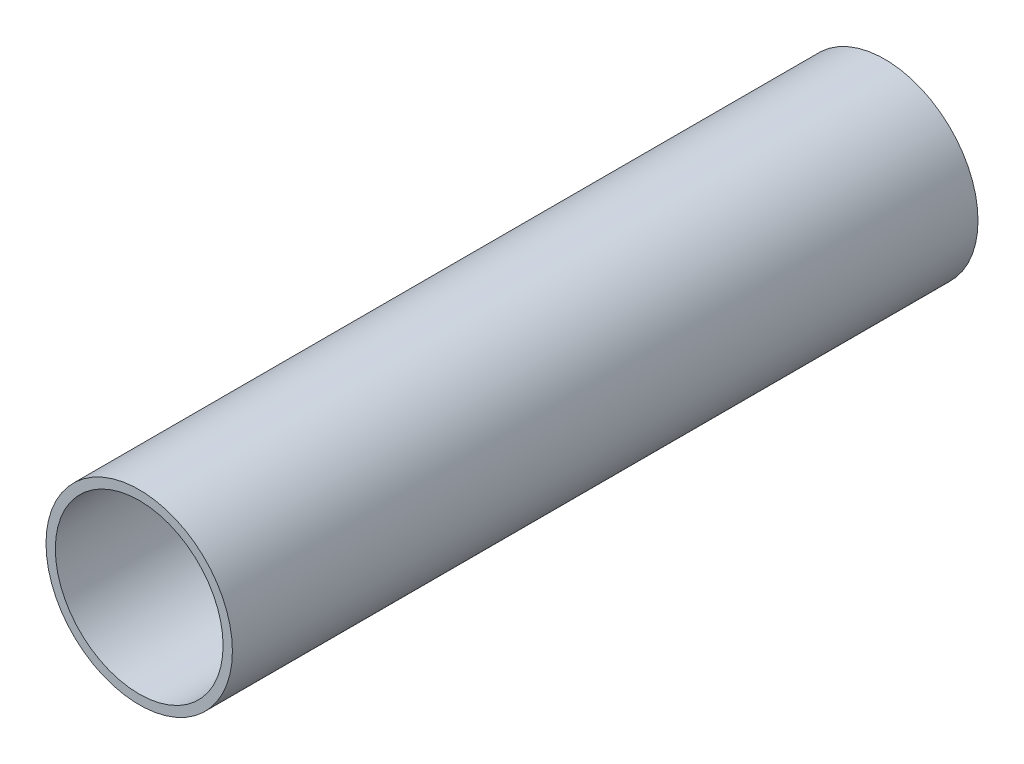
SolidWorks part; units mm, degrees
ref_plane "Front Plane" through (0, 0, 0) normal (0, 0, 1) x (1, 0, 0)
ref_plane "Top Plane" through (0, 0, 0) normal (0, 1, 0) x (1, 0, 0)
ref_plane "Right Plane" through (0, 0, 0) normal (1, 0, 0) x (0, 0, -1)
sketch "Sketch1" plane through (0, 0, 0) normal (0, 0, 1) x (1, 0, 0)
  circle A0 centre (0, 0) radius 45
  circle A1 centre (0, 0) radius 50
  dimension "D1" = 100
  dimension "D2" = 90
extrude "Boss-Extrude1" add sketch "Sketch1" along normal blind 400
